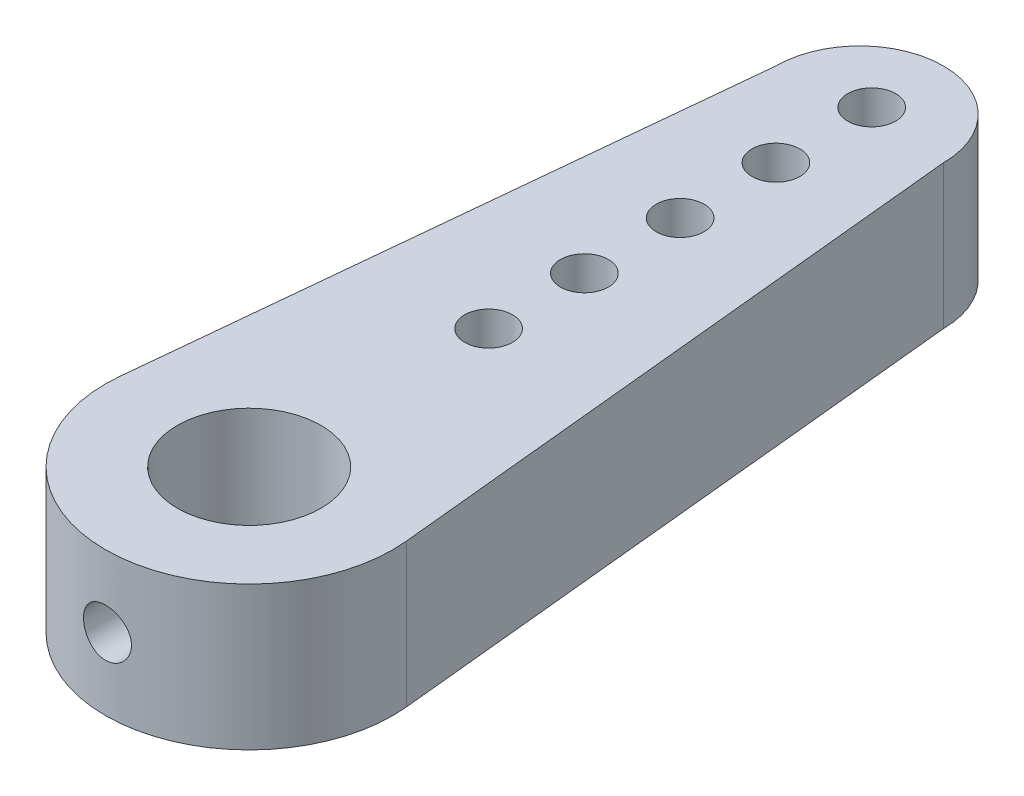
SolidWorks part; units mm, degrees
ref_plane "Front" through (0, 0, 0) normal (0, 0, 1) x (1, 0, 0)
ref_plane "Top" through (0, 0, 0) normal (0, 1, 0) x (1, 0, 0)
ref_plane "Right" through (0, 0, 0) normal (1, 0, 0) x (0, 0, -1)
sketch "Sketch1" plane through (0, 0, 0) normal (0, 1, 0) x (1, 0, 0)
  line L0 (0, 0) -> (0, 12.75) construction
  line L1 (-1.75, 12.75) -> (-2.9853, 0.2961)
  line L2 (1.75, 12.75) -> (2.9853, 0.2961)
  line L3 (0, 12.75) -> (0, 13) construction
  circle A0 centre (0, 0) radius 1.5
  arc A1 (-2.9853, 0.2961) -> (2.9853, 0.2961) centre (0, 0) ccw
  arc A2 (1.75, 12.75) -> (-1.75, 12.75) centre (0, 12.75) ccw
  circle A3 centre (0, 0) radius 3 construction
  circle A4 centre (0, 5) radius 0.5
  circle A5 centre (0, 7) radius 0.5
  circle A6 centre (0, 9) radius 0.5
  circle A7 centre (0, 11) radius 0.5
  circle A8 centre (0, 13) radius 0.5
  point P13 (0, 0)
  point P21 (0, 14.5)
  dimension "D1" = 3
  dimension "D3" = 3.5
  dimension "D5" = 1
  dimension "D4" = 12.75
  dimension "D7" = 1.5
  dimension "D2" = 1.5
  dimension "D6" = 5
extrude "Boss-Extrude1" add sketch "Sketch1" along normal blind 3
ref_plane "Plane1" through (0, 0, 3) normal (0, 0, 1) x (1, 0, 0)
sketch "Sketch2" plane through (0, 0, 3) normal (0, 0, 1) x (1, 0, 0)
  line L0 (0, 0) -> (0, 3) construction
  line L1 (3, 3) -> (-3, 3) construction
  circle A0 centre (0, 1.5) radius 0.5
  dimension "D1" = 1
extrude "Cut-Extrude1" cut sketch "Sketch2" against normal blind 3
